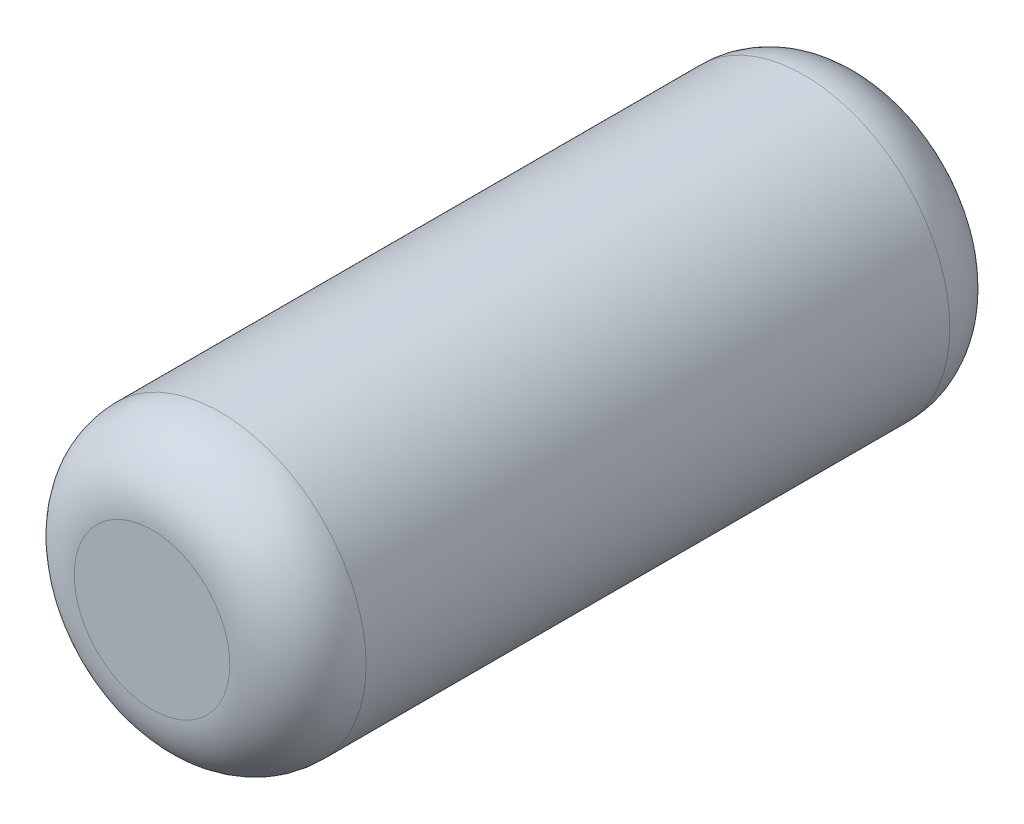
SolidWorks part; units mm, degrees
ref_plane "Front" through (0, 0, 0) normal (0, 0, 1) x (1, 0, 0)
ref_plane "Top" through (0, 0, 0) normal (0, 1, 0) x (1, 0, 0)
ref_plane "Right" through (0, 0, 0) normal (1, 0, 0) x (0, 0, -1)
sketch "Sketch1" plane through (0, 0, 0) normal (0, 0, 1) x (1, 0, 0)
  circle A0 centre (0, 0) radius 0.75
  dimension "D1" = 1.5
extrude "Boss-Extrude1" add sketch "Sketch1" along normal mid plane 3.7
fillet "Fillet1" radius 0.35 2 edges at (0.75, 0, -1.85) (0.75, 0, 1.85)
